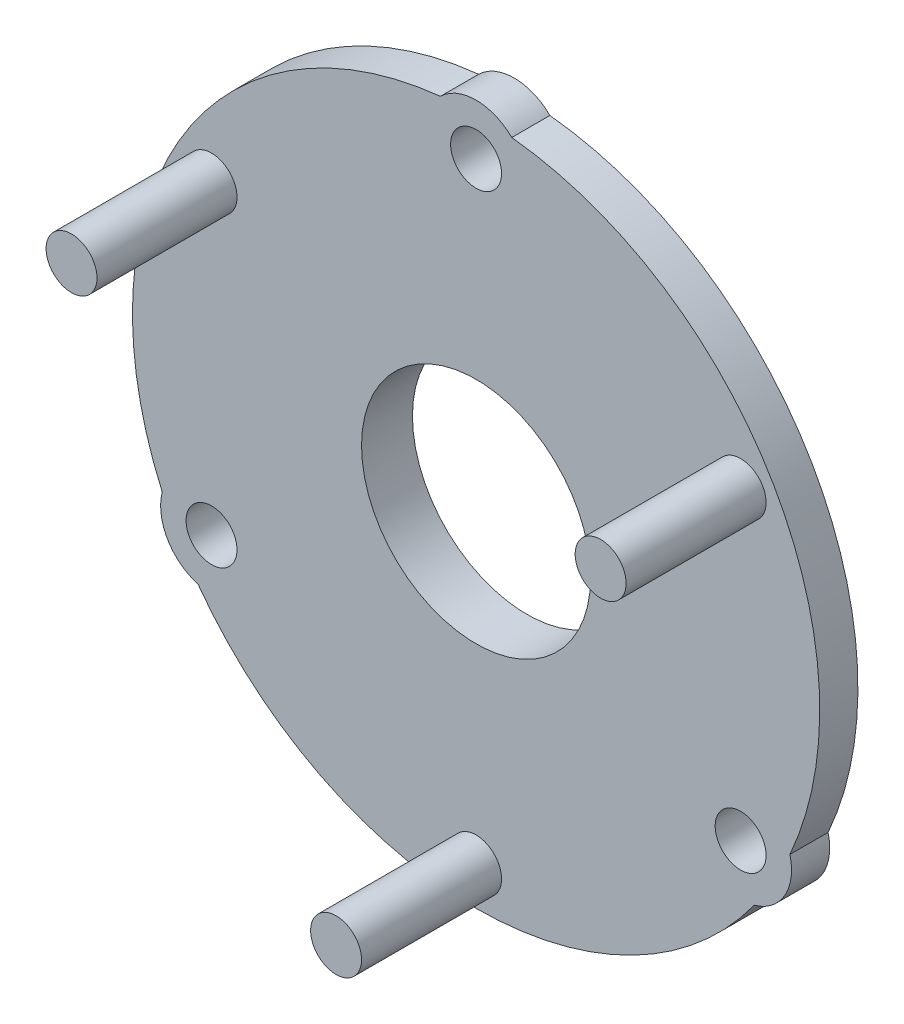
SolidWorks part; units mm, degrees
ref_plane "Plane1" through (0, 0, 0) normal (0, 0, 1) x (1, 0, 0)
ref_plane "Plane2" through (0, 0, 0) normal (0, 1, 0) x (1, 0, 0)
ref_plane "Plane3" through (0, 0, 0) normal (1, 0, 0) x (0, 0, -1)
sketch "Esquisse1" plane through (0, 0, 0) normal (0, 0, 1) x (1, 0, 0)
  line L0 (0, 0) -> (0, 19) construction
  arc A0 (12.3288, -5.5) -> (1.4012, 13.4271) centre (0, 0) ccw
  arc A1 (1.4012, 13.4271) -> (-1.4012, 13.4271) centre (0, 12) ccw
  arc A2 (10.9276, -7.927) -> (12.3288, -5.5) centre (10.3923, -6) ccw
  arc A3 (-12.3288, -5.5) -> (-10.9276, -7.927) centre (-10.3923, -6) ccw
  arc A4 (-1.4012, 13.4271) -> (-12.3288, -5.5) centre (0, 0) ccw
  arc A5 (-10.9276, -7.927) -> (10.9276, -7.927) centre (0, 0) ccw
  dimension "D1" = 27
  dimension "D2" = 4
  dimension "D3" = 12
extrude "Base-Extrusion" add sketch "Esquisse1" along normal blind 1.5
sketch "Esquisse2" plane through (0, 0, 1.5) normal (0, 0, 1) x (1, 0, 0)
  circle A0 centre (0, 12) radius 1
  circle A1 centre (10.3923, -6) radius 1
  circle A2 centre (-10.3923, -6) radius 1
  dimension "D1" = 2
extrude "Enlèv. mat.-Extru.1" cut sketch "Esquisse2" against normal through all
sketch "Esquisse3" plane through (0, 0, 1.5) normal (0, 0, 1) x (1, 0, 0)
  line L0 (0, 0) -> (17.0807, 9.8615) construction
  line L1 (0, 0) -> (18, 0) construction
  circle A0 centre (10.3923, 6) radius 1
  circle A1 centre (0, -12) radius 1
  circle A2 centre (-10.3923, 6) radius 1
  dimension "D2" = 2
  dimension "D1" = 30
  dimension "D3" = 12
extrude "Boss.-Extru.1" add sketch "Esquisse3" along normal blind 5.5
sketch "Esquisse4" plane through (0, 0, 0) normal (0, 0, -1) x (-1, 0, 0)
  circle A0 centre (0, 0) radius 6
  dimension "D1" = 12
extrude "Boss.-Extru.2" add sketch "Esquisse4" along normal blind 0.5
sketch "Esquisse5" plane through (0, 0, -0.5) normal (0, 0, -1) x (-1, 0, 0)
  circle A0 centre (0, 0) radius 4.5
  dimension "D1" = 9
extrude "Enlèv. mat.-Extru.2" cut sketch "Esquisse5" against normal through all
